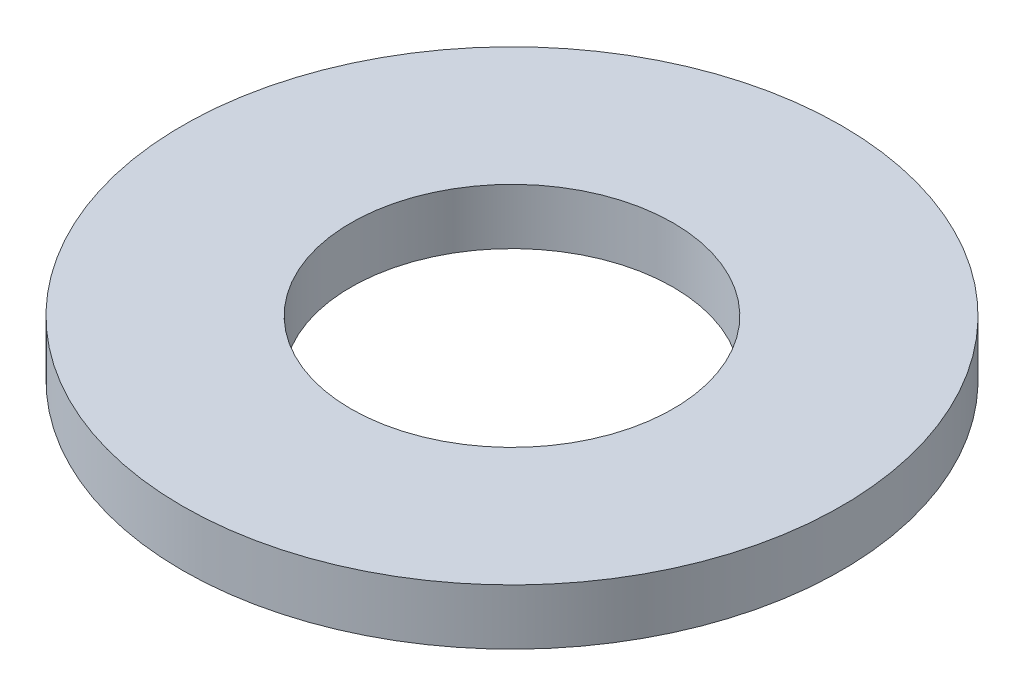
SolidWorks part; units mm, degrees
material "Alloy Steel"
ref_plane "Front Plane" through (0, 0, 0) normal (0, 0, 1) x (1, 0, 0)
ref_plane "Top Plane" through (0, 0, 0) normal (0, 1, 0) x (1, 0, 0)
ref_plane "Right Plane" through (0, 0, 0) normal (1, 0, 0) x (0, 0, -1)
sketch "Sketch2" plane through (0, 0, 0) normal (0, 1, 0) x (1, 0, 0)
  circle A0 centre (0, 0) radius 4.5
  circle A1 centre (0, 0) radius 2.2
  dimension "D1" = 4.4
  dimension "D2" = 9
extrude "Boss-Extrude1" add sketch "Sketch2" along normal blind 0.76
